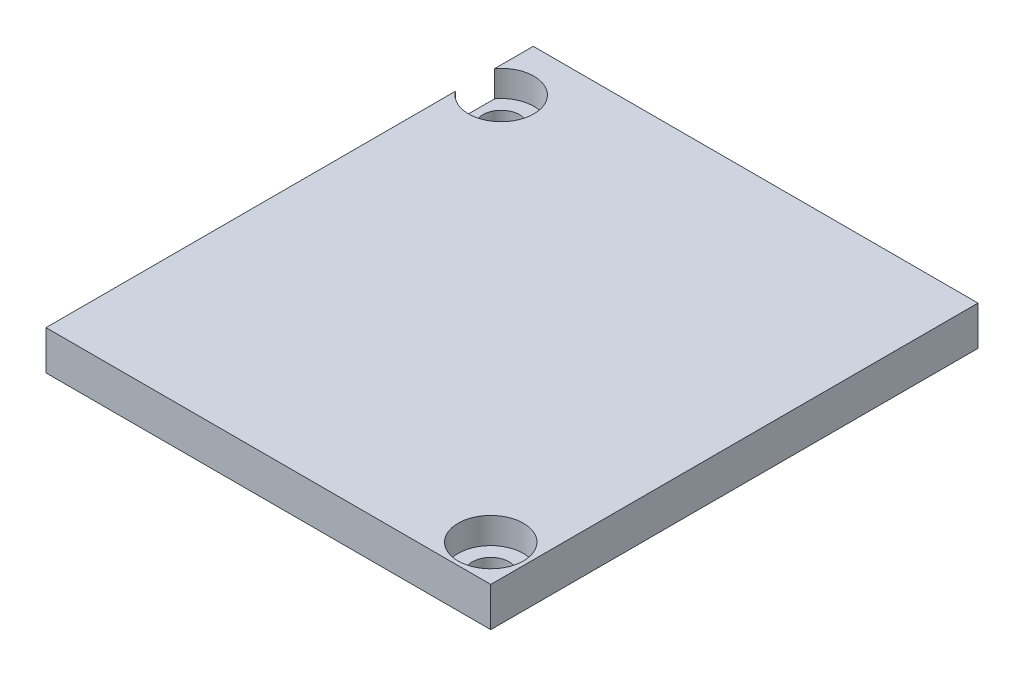
SolidWorks part; units mm, degrees
ref_plane "Front Plane" through (0, 0, 0) normal (0, 0, 1) x (1, 0, 0)
ref_plane "Top Plane" through (0, 0, 0) normal (0, 1, 0) x (1, 0, 0)
ref_plane "Right Plane" through (0, 0, 0) normal (1, 0, 0) x (0, 0, -1)
sketch "Sketch1" plane through (0, 0, 0) normal (0, 1, 0) x (1, 0, 0)
  line L1 (-17, -18.625) -> (17, -18.625)
  line L2 (-17, -18.625) -> (-17, 18.625)
  line L3 (-17, 18.625) -> (17, 18.625)
  line L4 (17, -18.625) -> (17, 18.625)
  line L5 (-17, -18.625) -> (17, 18.625) construction
  line L6 (-17, 18.625) -> (17, -18.625) construction
  point P0 (0, 0)
  dimension "D1" = 34
  dimension "D2" = 37.25
extrude "Boss-Extrude1" add sketch "Sketch1" along normal blind 3
sketch "Sketch2" plane through (0, 3, 0) normal (0, 1, 0) x (1, 0, 0)
  line L0 (17, -18.625) -> (17, 18.625) construction
  line L1 (-17, -18.625) -> (17, -18.625) construction
  line L2 (-17, 18.625) -> (-17, -18.625) construction
  line L3 (17, 18.625) -> (-17, 18.625) construction
  circle A0 centre (-15, 14.175) radius 2.5
  circle A1 centre (14.2, -15.825) radius 2.5
  dimension "D1" = 2.8
  dimension "D2" = 2.8
  dimension "D3" = 2
  dimension "D4" = 4.45
  dimension "D5" = 5
  dimension "D6" = 5
extrude "Cut-Extrude1" cut sketch "Sketch2" against normal blind 2
sketch "Sketch3" plane through (0, 1, 0) normal (0, 1, 0) x (1, 0, 0)
  circle A0 centre (-15, 14.175) radius 1.4
  circle A1 centre (14.2, -15.825) radius 1.4
  dimension "D1" = 2.8
  dimension "D2" = 2.8
extrude "Cut-Extrude2" cut sketch "Sketch3" against normal blind 2
